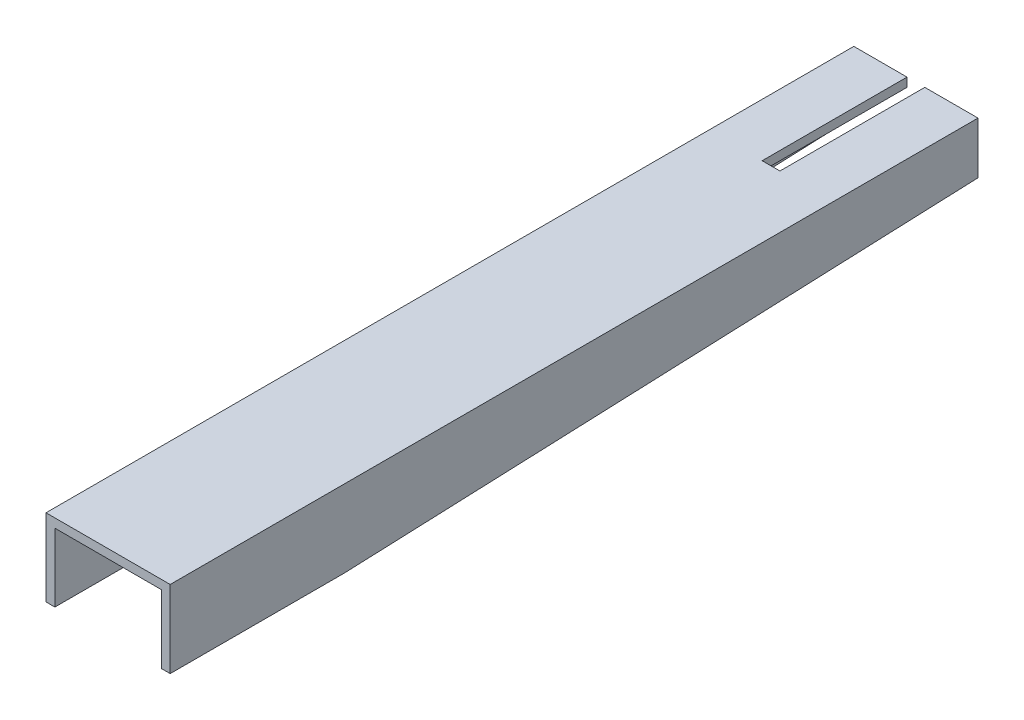
SolidWorks part; units mm, degrees
ref_plane "Front Plane" through (0, 0, 0) normal (0, 0, 1) x (1, 0, 0)
ref_plane "Top Plane" through (0, 0, 0) normal (0, 1, 0) x (1, 0, 0)
ref_plane "Right Plane" through (0, 0, 0) normal (1, 0, 0) x (0, 0, -1)
sketch "Sketch1" plane through (0, 0, 0) normal (0, 0, 1) x (1, 0, 0)
  line L0 (-30, 0) -> (-25.7, 0)
  line L5 (-25.7, 0) -> (-25.7, 20.7)
  line L6 (-25.7, 20.7) -> (25.7, 20.7)
  line L7 (25.7, 20.7) -> (25.7, 0)
  line L8 (25.7, 0) -> (30, 0)
  line L9 (30, 0) -> (30, 25)
  line L10 (30, 25) -> (-30, 25)
  line L11 (-30, 25) -> (-30, 0)
  point P9 (0, 20.7)
  dimension "D1" = 4.3
  dimension "D2" = 4.3
  dimension "D3" = 60
  dimension "D4" = 25
extrude "Boss-Extrude1" add sketch "Sketch1" along normal blind 390.3
sketch "Sketch2" plane through (30, 0, 0) normal (1, 0, 0) x (0, 0, -1)
  line L0 (-306, 0) -> (-306, -12.31) construction
  line L1 (-306, -12.31) -> (0, 0)
  line L2 (0, 0) -> (-390.3, 0)
  line L3 (-390.3, 0) -> (-390.3, -12.31)
  line L4 (-390.3, -12.31) -> (-306, -12.31)
  dimension "D1" = 306
  dimension "D2" = 12.31
extrude "Boss-Extrude2" add sketch "Sketch2" against normal blind 4.3
mirror "Mirror1" about plane through (0, 0, 0) normal (1, 0, 0) of "Boss-Extrude2"
sketch "Sketch3" plane through (0, 25, 0) normal (0, 1, 0) x (1, 0, 0)
  line L0 (-20.5205, 0) -> (20.5205, 0) construction
  line L1 (-4.3, 0) -> (4.3, 0)
  line L2 (-4.3, 0) -> (-4.3, -70)
  line L3 (-4.3, -70) -> (4.3, -70)
  line L4 (4.3, 0) -> (4.3, -70)
  line L5 (0, -20.5205) -> (0, 20.5205) construction
  point P6 (0, 0)
  dimension "D1" = 70
  dimension "D2" = 8.6
extrude "Cut-Extrude1" cut sketch "Sketch3" against normal blind 10
sketch "Sketch4" plane through (0, 25, 0) normal (0, 1, 0) x (1, 0, 0)
  line L0 (30, -390.3) -> (-30, -390.3) construction
  line L1 (-72.4089, 43.2578) -> (158.3943, 43.2578)
  line L2 (-72.4089, 43.2578) -> (-72.4089, -306)
  line L3 (-72.4089, -306) -> (158.3943, -306)
  line L4 (158.3943, 43.2578) -> (158.3943, -306)
  dimension "D1" = 84.3
extrude "Cut-Extrude2" [suppressed] cut sketch "Sketch4" against normal blind 15
sketch "Sketch5" plane through (-30, 0, 0) normal (-1, 0, 0) x (0, 0, 1)
  line L0 (0, 0) -> (306, -12.31)
  line L1 (306, -12.31) -> (390.3, -12.31)
  line L2 (390.3, -12.31) -> (390.3, 20)
  line L3 (390.3, 25) -> (390.3, -12.31) construction
  line L4 (390.3, 20) -> (0, 20)
  line L5 (0, -20.5205) -> (0, 20.5205) construction
  line L6 (0, 20) -> (0, 0)
  line L7 (390.3, 25) -> (0, 25) construction
  dimension "D1" = 5
